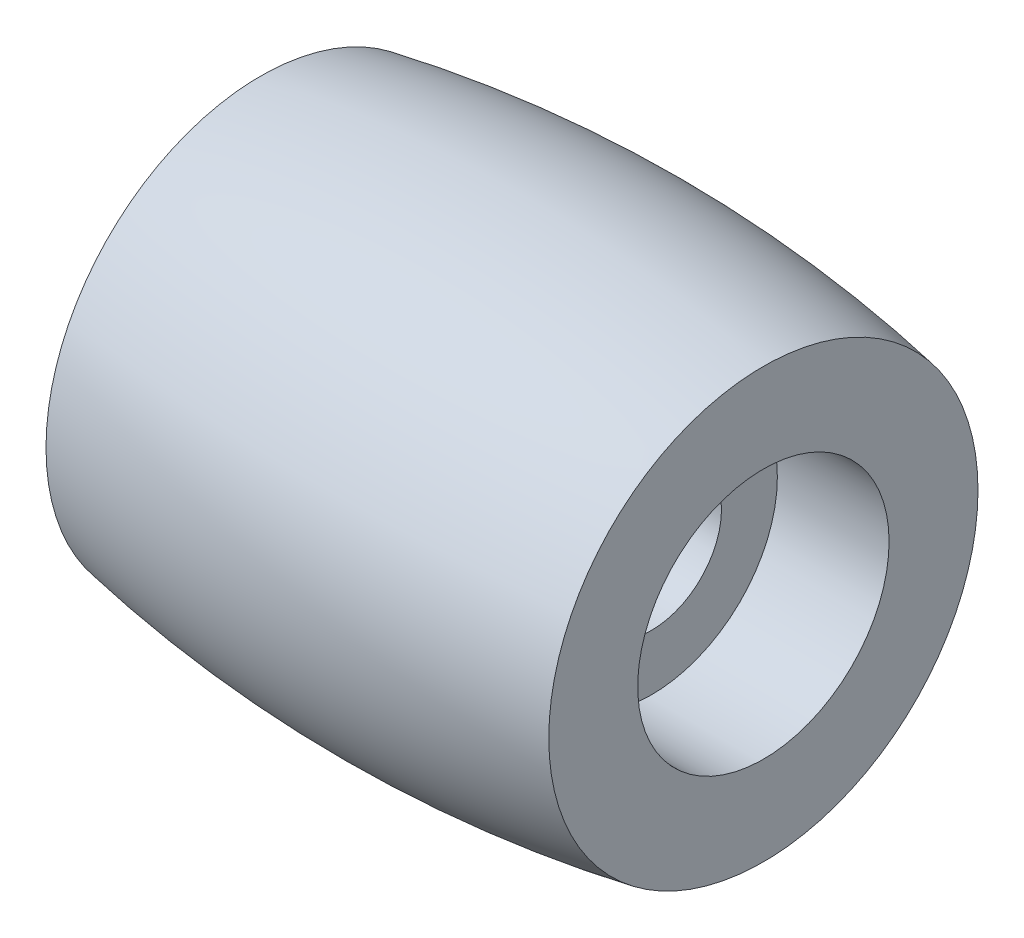
SolidWorks part; units mm, degrees
other "攝影機1"
material "矽膠"
ref_plane "前基準面" through (0, 0, 0) normal (0, 0, 1) x (1, 0, 0)
ref_plane "上基準面" through (0, 0, 0) normal (0, 1, 0) x (1, 0, 0)
ref_plane "右基準面" through (0, 0, 0) normal (1, 0, 0) x (0, 0, -1)
sketch "草圖1" plane through (0, 0, 0) normal (0, 0, 1) x (1, 0, 0)
  line L0 (-9, 0) -> (9, 0)
  line L1 (9, 0) -> (9, 7.6833)
  line L2 (-9, 0) -> (-9, 7.6833)
  arc A0 (-9, 7.6833) -> (9, 7.6833) centre (0, -41.5) cw
  point P4 (0, 0)
  point P7 (0, 8.5)
  dimension "D2" = 50
  dimension "D1" = 18
  dimension "D3" = 8.5
revolve "旋轉1" add sketch "草圖1" angle 360 about L0
sketch "草圖2" plane through (9, 0, 0) normal (1, 0, 0) x (0, 0, -1)
  circle A0 centre (0, 0) radius 2.5
  dimension "D1" = 5
extrude "除料-伸長1" cut sketch "草圖2" against normal through all
sketch "草圖3" plane through (9, 0, 0) normal (1, 0, 0) x (0, 0, -1)
  circle A0 centre (0, 0) radius 4.5
  dimension "D1" = 9
extrude "除料-伸長2" cut sketch "草圖3" against normal blind 4
mirror "鏡射1" about plane through (0, 0, 0) normal (1, 0, 0) of "除料-伸長2"
